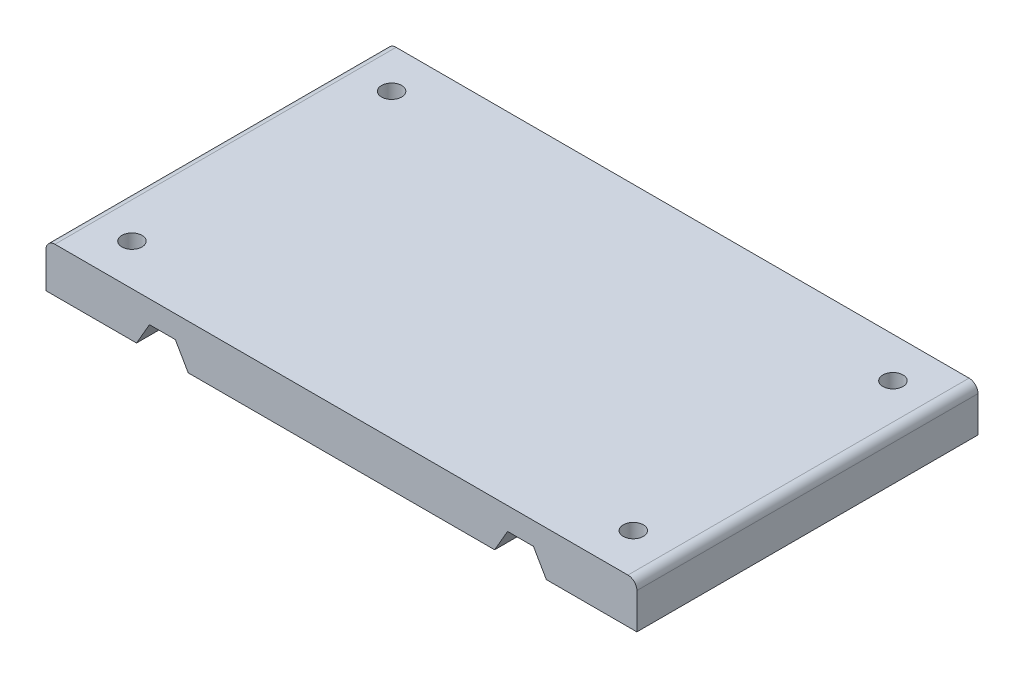
SolidWorks part; units mm, degrees
ref_plane "Front Plane" through (0, 0, 0) normal (0, 0, 1) x (1, 0, 0)
ref_plane "Top Plane" through (0, 0, 0) normal (0, 1, 0) x (1, 0, 0)
ref_plane "Right Plane" through (0, 0, 0) normal (1, 0, 0) x (0, 0, -1)
sketch "Sketch1" plane through (0, 0, 0) normal (0, 0, 1) x (1, 0, 0)
  line L1 (-66, 0) -> (66, 0)
  line L2 (-66, 0) -> (-66, 10)
  line L3 (-66, 10) -> (66, 10)
  line L4 (66, 0) -> (66, 10)
  point P4 (0, 0)
  dimension "D1" = 132
  dimension "D2" = 10
extrude "Boss-Extrude1" add sketch "Sketch1" along normal blind 76.2 contours L3 L4 L1 L2
sketch "Sketch2" plane through (0, 0, 76.2) normal (0, 0, 1) x (1, 0, 0)
  line L0 (-66, 0) -> (66, 0) construction
  line L7 (0, 0) -> (0, 19.3508) construction
  line L8 (34.2265, 0) -> (37.1132, -5)
  line L9 (37.1132, -5) -> (42.8868, -5)
  line L10 (42.8868, -5) -> (45.7735, 0)
  line L11 (45.7735, 0) -> (42.8868, 5)
  line L12 (42.8868, 5) -> (37.1132, 5)
  line L13 (37.1132, 5) -> (34.2265, 0)
  line L14 (-37.1132, 5) -> (-34.2265, 0)
  line L15 (-66, 0) -> (-66, 10) construction
  line L16 (-42.8868, 5) -> (-37.1132, 5)
  line L17 (-45.7735, 0) -> (-42.8868, 5)
  line L18 (-42.8868, -5) -> (-45.7735, 0)
  line L19 (-37.1132, -5) -> (-42.8868, -5)
  line L20 (-34.2265, 0) -> (-37.1132, -5)
  circle A0 centre (-40, 0) radius 5 construction
  circle A1 centre (40, 0) radius 5 construction
  dimension "D2" = 10
  dimension "D4" = 40
extrude "Cut-Extrude1" cut sketch "Sketch2" against normal blind 76.2
sketch "Sketch11" plane through (0, 10, 0) normal (0, 1, 0) x (1, 0, 0)
  line L0 (-66, -76.2) -> (-66, 0) construction
  line L1 (66, -76.2) -> (66, 0) construction
  line L2 (-66, 0) -> (66, 0) construction
  circle A0 centre (-56, -9) radius 4
  circle A1 centre (-56, -67) radius 4
  circle A2 centre (56, -9) radius 4
  circle A3 centre (56, -67) radius 4
  dimension "D1" = 8
  dimension "D2" = 10
  dimension "D3" = 10
  dimension "D4" = 9
  dimension "D5" = 9
  dimension "D6" = 58
fillet "Fillet2" radius 2 2 edges at (66, 10, 38.1) (-66, 10, 38.1)
hole_wizard "M4 Clearance Hole1" positions "Sketch12" profile "Sketch13" hole size "M4" standard "ANSI Metric" end condition through all
sketch "Sketch12" plane through (0, 10, 0) normal (0, 1, 0) x (1, 0, 0)
  point P0 (-56, -67)
  point P3 (-56, -9)
  point P6 (56, -9)
  point P9 (56, -67)
sketch "Sketch13" plane through (-56, 10, 67) normal (1, 0, 0) x (0, 0, 1)
  line L0 (0, 0) -> (0, 10)
  line L1 (0, 10) -> (2.25, 10)
  line L2 (2.25, 10) -> (2.25, 0)
  line L5 (2.25, 0) -> (0, 0)
  line L11 (0, -6.35) -> (0, 107.95) construction
  dimension "Thru Hole Dia." = 4.5
  dimension "Thru Hole Depth" = 10
